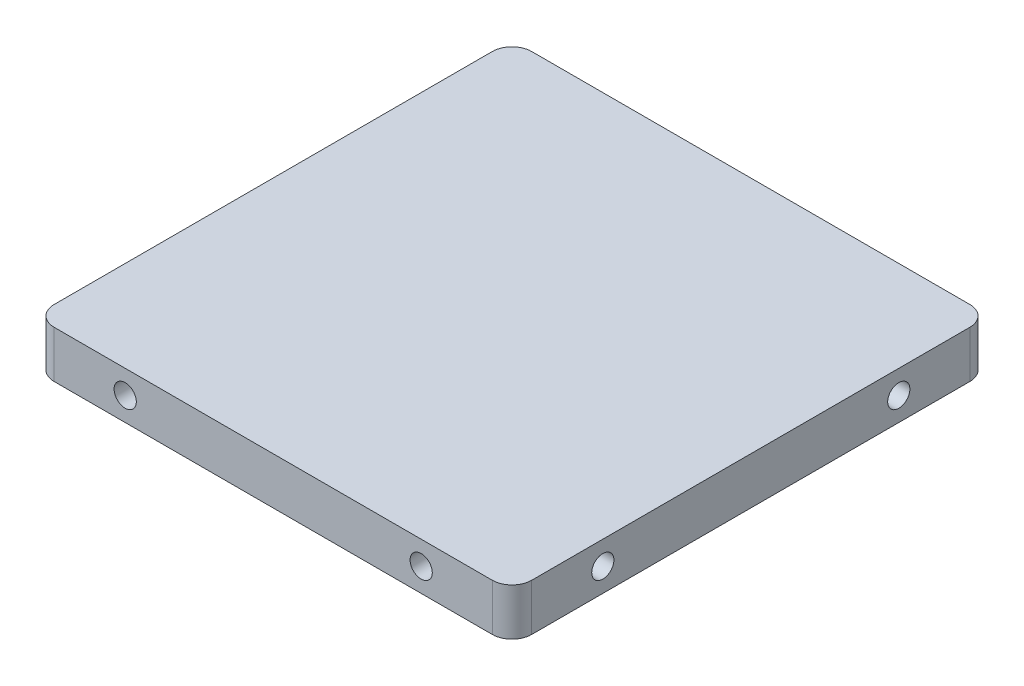
SolidWorks part; units mm, degrees
material "6061-T6 (SS)"
ref_plane "Front Plane" through (0, 0, 0) normal (0, 0, 1) x (1, 0, 0)
ref_plane "Top Plane" through (0, 0, 0) normal (0, 1, 0) x (1, 0, 0)
ref_plane "Right Plane" through (0, 0, 0) normal (1, 0, 0) x (0, 0, -1)
sketch "Sketch1" plane through (0, 0, 0) normal (0, 1, 0) x (1, 0, 0)
  line L1 (48.4125, -48.4125) -> (-48.4125, -48.4125)
  line L2 (48.4125, -48.4125) -> (48.4125, 48.4125)
  line L3 (48.4125, 48.4125) -> (-48.4125, 48.4125)
  line L4 (-48.4125, -48.4125) -> (-48.4125, 48.4125)
  line L5 (48.4125, -48.4125) -> (-48.4125, 48.4125) construction
  line L6 (48.4125, 48.4125) -> (-48.4125, -48.4125) construction
  point P0 (0, 0)
  dimension "D1" = 96.825
extrude "Boss-Extrude1" add sketch "Sketch1" along normal mid plane 9.525
fillet "Fillet1" radius 4 4 edges at (-48.4125, 0, -48.4125) (48.4125, 0, -48.4125) (48.4125, 0, 48.4125) (-48.4125, 0, 48.4125)
sketch "Sketch4" plane through (-48.4125, 0, 0) normal (-1, 0, 0) x (0, 0, 1)
  point P0 (-30, 0)
  point P2 (30, 0)
  point P6 (0, 0)
  point P7 (0, 0)
  dimension "D1" = 30
  dimension "D2" = 30
hole_wizard "M4 Clearance Hole1" positions "Sketch4" profile "Sketch3" hole size "M4" standard "ANSI Metric" end condition through all
sketch "Sketch3" plane through (-48.4125, 0, -30) normal (0, 1, 0) x (0, 0, 1)
  line L0 (0, 0) -> (0, 96.825)
  line L1 (0, 96.825) -> (2.25, 96.825)
  line L2 (2.25, 96.825) -> (2.25, 0)
  line L5 (2.25, 0) -> (0, 0)
  line L11 (0, -6.35) -> (0, 107.95) construction
  dimension "Thru Hole Dia." = 4.5
  dimension "Thru Hole Depth" = 96.825
sketch "Sketch7" plane through (0, 0, -48.4125) normal (0, 0, -1) x (-1, 0, 0)
  point P0 (-30, 0)
  point P2 (30, 0)
  point P6 (0, 0)
  dimension "D1" = 30
  dimension "D2" = 30
hole_wizard "M4 Clearance Hole2" positions "Sketch7" profile "Sketch6" hole size "M4" standard "ANSI Metric" end condition through all
sketch "Sketch6" plane through (30, 0, -48.4125) normal (1, 0, 0) x (0, 1, 0)
  line L0 (0, 0) -> (0, 96.825)
  line L1 (0, 96.825) -> (2.25, 96.825)
  line L2 (2.25, 96.825) -> (2.25, 0)
  line L5 (2.25, 0) -> (0, 0)
  line L11 (0, -6.35) -> (0, 107.95) construction
  dimension "Thru Hole Dia." = 4.5
  dimension "Thru Hole Depth" = 96.825
